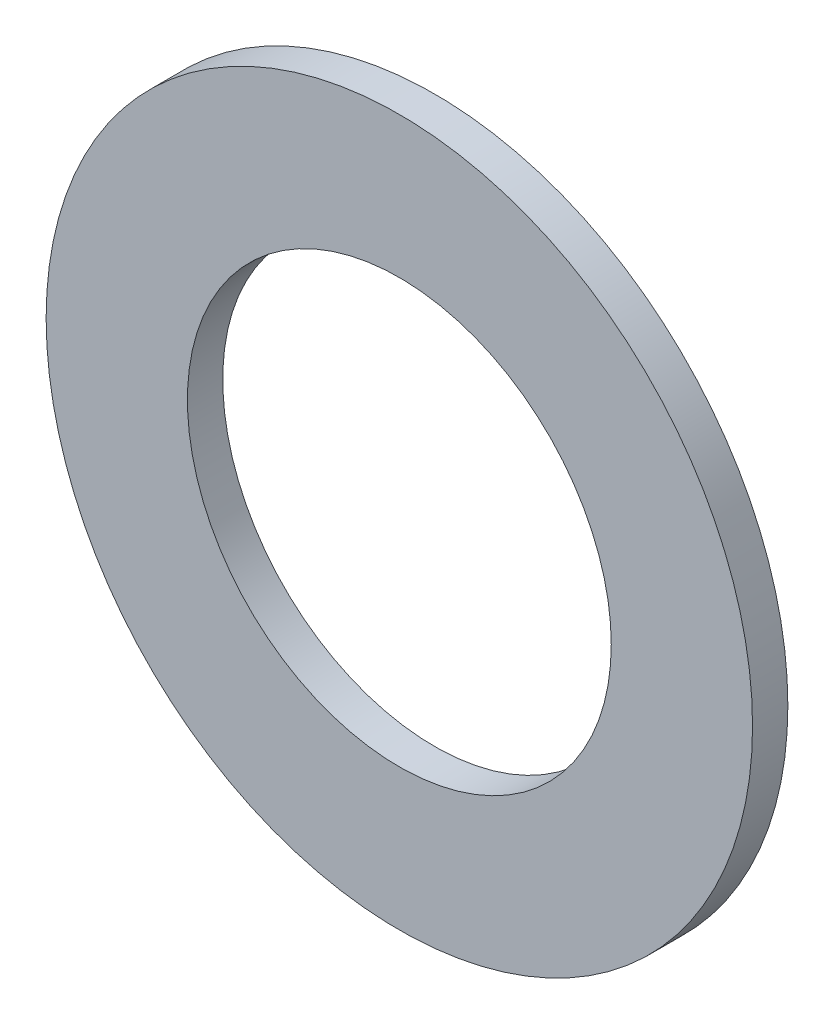
SolidWorks part; units mm, degrees
ref_plane "Front Plane" through (0, 0, 0) normal (0, 0, 1) x (1, 0, 0)
ref_plane "Top Plane" through (0, 0, 0) normal (0, 1, 0) x (1, 0, 0)
ref_plane "Right Plane" through (0, 0, 0) normal (1, 0, 0) x (0, 0, -1)
sketch "Sketch1" plane through (0, 0, 0) normal (0, 0, 1) x (1, 0, 0)
  circle A0 centre (0, 0) radius 12.7
  circle A2 centre (0, 0) radius 7.62
extrude "Boss-Extrude1" add sketch "Sketch1" along normal blind 1.27
